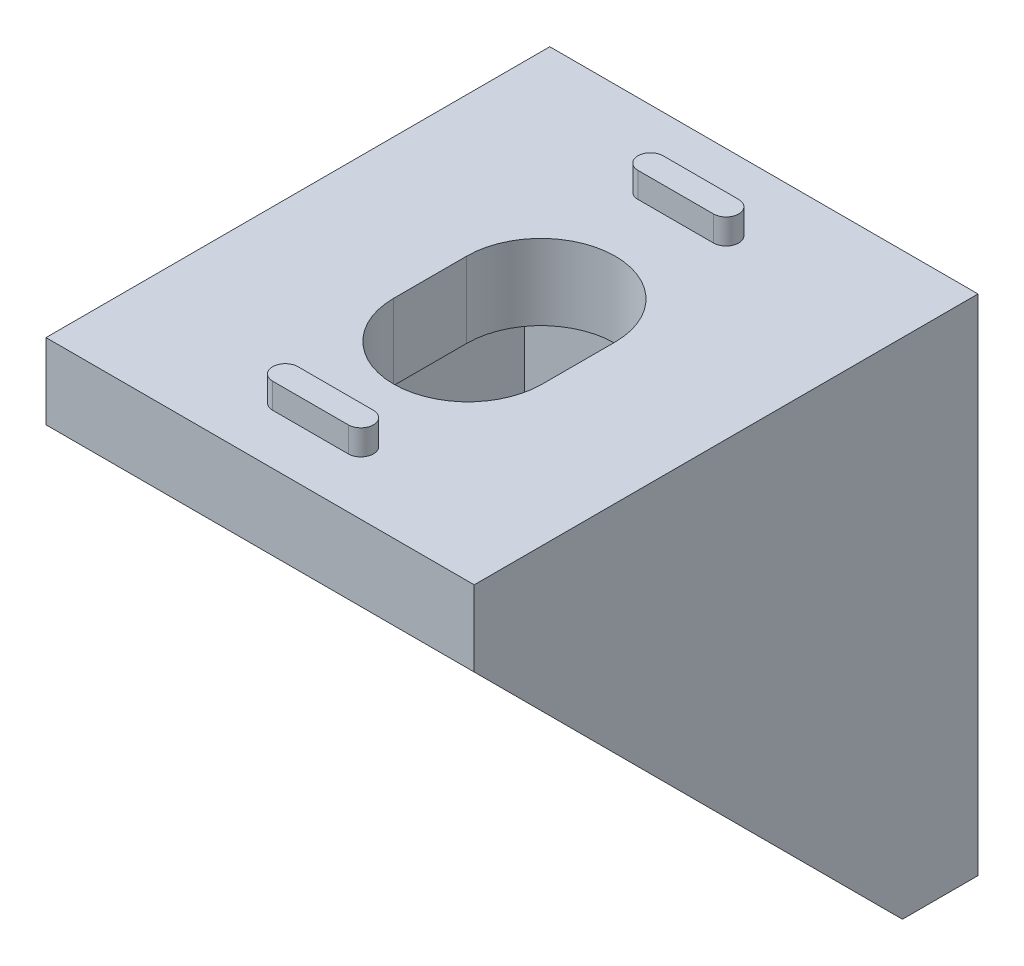
SolidWorks part; units mm, degrees
material "356.0-T6 永久成型铸件 (SS)"
ref_plane "前视基准面" through (0, 0, 0) normal (0, 0, 1) x (1, 0, 0)
ref_plane "上视基准面" through (0, 0, 0) normal (0, 1, 0) x (1, 0, 0)
ref_plane "右视基准面" through (0, 0, 0) normal (1, 0, 0) x (0, 0, -1)
sketch "草图1" plane through (0, 0, 0) normal (0, 0, 1) x (1, 0, 0)
  line L1 (-8.5, -10) -> (8.5, -10)
  line L2 (-8.5, -10) -> (-8.5, 10)
  line L3 (-8.5, 10) -> (8.5, 10)
  line L4 (8.5, -10) -> (8.5, 10)
  line L5 (-8.5, -10) -> (8.5, 10) construction
  line L6 (-8.5, 10) -> (8.5, -10) construction
  point P0 (0, 0)
  dimension "D1" = 17
  dimension "D2" = 20
extrude "凸台-拉伸1" add sketch "草图1" along normal blind 3
sketch "草图2" plane through (0, 0, 3) normal (0, 0, 1) x (1, 0, 0)
  line L0 (8.5, -10) -> (8.5, 10) construction
  line L1 (-8.5, 10) -> (8.5, 10)
  line L2 (-8.5, 10) -> (-8.5, 7)
  line L3 (-8.5, 7) -> (8.5, 7)
  line L4 (8.5, 10) -> (8.5, 7)
  dimension "D1" = 3
extrude "凸台-拉伸2" add sketch "草图2" along normal blind 17
sketch "草图3" plane through (-8.5, 0, 0) normal (-1, 0, 0) x (0, 0, 1)
  line L0 (20, 7) -> (3, -10)
  line L1 (3, -10) -> (3, 7)
  line L2 (3, 7) -> (20, 7)
extrude "凸台-拉伸3" add sketch "草图3" against normal blind 2
sketch "草图4" plane through (8.5, 0, 0) normal (1, 0, 0) x (0, 0, -1)
  line L0 (-20, 7) -> (-3, -10)
  line L1 (-3, -10) -> (-3, 7)
  line L2 (-3, 7) -> (-20, 7)
extrude "凸台-拉伸4" add sketch "草图4" against normal blind 2
sketch "草图5" plane through (0, 10, 0) normal (0, 1, 0) x (1, 0, 0)
  line L0 (0, 0) -> (0, -20) construction
  line L1 (8.5, -20) -> (-8.5, -20) construction
  line L2 (-1.5, -3) -> (1.5, -3) construction
  line L3 (-1.5, -2.5) -> (1.5, -2.5)
  line L4 (-1.5, -3.5) -> (1.5, -3.5)
  line L5 (-1.5, -17.5) -> (1.5, -17.5) construction
  line L6 (-1.5, -17) -> (1.5, -17)
  line L7 (-1.5, -18) -> (1.5, -18)
  line L8 (8.5, 0) -> (-8.5, 0) construction
  arc A0 (-1.5, -2.5) -> (-1.5, -3.5) centre (-1.5, -3) ccw
  arc A1 (1.5, -3.5) -> (1.5, -2.5) centre (1.5, -3) ccw
  arc A2 (-1.5, -17) -> (-1.5, -18) centre (-1.5, -17.5) ccw
  arc A3 (1.5, -18) -> (1.5, -17) centre (1.5, -17.5) ccw
  point P7 (0, -3)
  point P12 (0, -17.5)
  dimension "D2" = 0.5
  dimension "D6" = 0.5
  dimension "D1" = 3
  dimension "D3" = 1.5
  dimension "D4" = 3
  dimension "D5" = 2.5
  dimension "D7" = 3
  dimension "D8" = 1.5
extrude "凸台-拉伸5" add sketch "草图5" along normal blind 1
sketch "草图6" plane through (0, 0, 0) normal (0, 0, -1) x (-1, 0, 0)
  line L0 (0, 10) -> (0, -10.0828) construction
  line L1 (-1.5, 7) -> (1.5, 7) construction
  line L2 (-1.5, 7.5) -> (1.5, 7.5)
  line L3 (-1.5, 6.5) -> (1.5, 6.5)
  line L4 (-1.5, -7.5) -> (1.5, -7.5) construction
  line L5 (-1.5, -7) -> (1.5, -7)
  line L6 (-1.5, -8) -> (1.5, -8)
  line L7 (-8.5, 10) -> (8.5, 10) construction
  line L8 (8.5, -10) -> (-8.5, -10) construction
  arc A0 (-1.5, 7.5) -> (-1.5, 6.5) centre (-1.5, 7) ccw
  arc A1 (1.5, 6.5) -> (1.5, 7.5) centre (1.5, 7) ccw
  arc A2 (-1.5, -7) -> (-1.5, -8) centre (-1.5, -7.5) ccw
  arc A3 (1.5, -8) -> (1.5, -7) centre (1.5, -7.5) ccw
  point P4 (0, 7)
  point P9 (0, -7.5)
  point P16 (0, 10)
  dimension "D2" = 0.5
  dimension "D4" = 0.5
  dimension "D1" = 3
  dimension "D3" = 1.5
  dimension "D5" = 3
  dimension "D6" = 1.5
  dimension "D7" = 3
  dimension "D8" = 2.5
extrude "凸台-拉伸6" add sketch "草图6" along normal blind 1
sketch "草图7" plane through (0, 0, 0) normal (0, 0, -1) x (-1, 0, 0)
  line L0 (0, 10) -> (0, -10) construction
  line L1 (-8.5, 10) -> (8.5, 10) construction
  line L2 (8.5, -10) -> (-8.5, -10) construction
  line L3 (0, 1.15) -> (0, -1.75) construction
  line L4 (2.95, 1.15) -> (2.95, -1.75)
  line L5 (-2.95, 1.15) -> (-2.95, -1.75)
  arc A0 (2.95, 1.15) -> (-2.95, 1.15) centre (0, 1.15) ccw
  arc A1 (-2.95, -1.75) -> (2.95, -1.75) centre (0, -1.75) ccw
  point P8 (0, -0.3)
  point P13 (0, 4.1)
  dimension "D2" = 2.9
  dimension "D1" = 5.9
  dimension "D3" = 5.9
extrude "切除-拉伸3" cut sketch "草图7" against normal through all
sketch "草图8" plane through (0, 10, 0) normal (0, 1, 0) x (1, 0, 0)
  line L0 (0, -0.6756) -> (0, -20) construction
  line L1 (0, -8.85) -> (0, -11.75) construction
  line L2 (2.95, -8.85) -> (2.95, -11.75)
  line L3 (-2.95, -8.85) -> (-2.95, -11.75)
  line L4 (8.5, -20) -> (-8.5, -20) construction
  arc A0 (2.95, -8.85) -> (-2.95, -8.85) centre (0, -8.85) ccw
  arc A1 (-2.95, -11.75) -> (2.95, -11.75) centre (0, -11.75) ccw
  point P4 (0, -10.3)
  point P9 (0, -5.9)
  point P10 (0, -20)
  dimension "D1" = 5.9
  dimension "D2" = 2.9
  dimension "D3" = 5.9
extrude "切除-拉伸4" cut sketch "草图8" against normal through all
